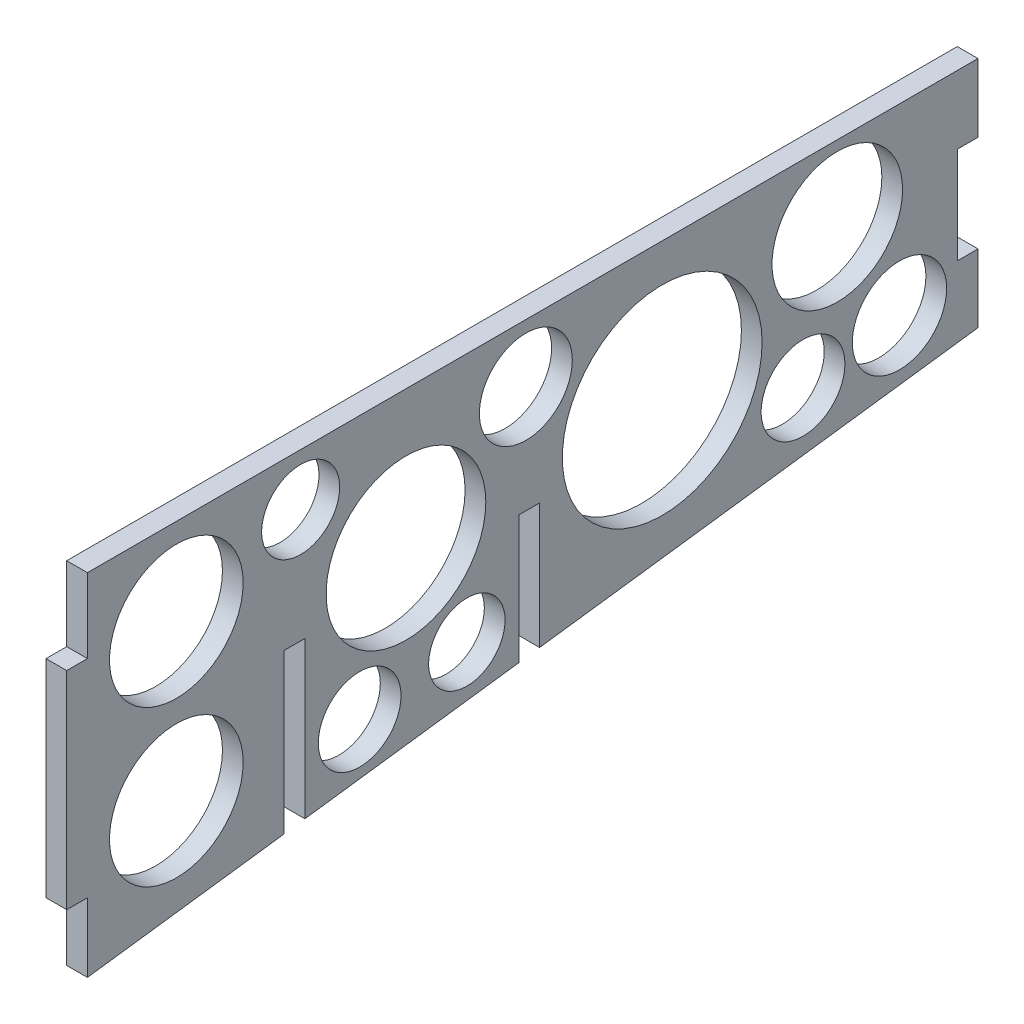
SolidWorks part; units mm, degrees
ref_plane "Front Plane" through (0, 0, 0) normal (0, 0, 1) x (1, 0, 0)
ref_plane "Top Plane" through (0, 0, 0) normal (0, 1, 0) x (1, 0, 0)
ref_plane "Right Plane" through (0, 0, 0) normal (1, 0, 0) x (0, 0, -1)
sketch "Sketch1" plane through (0, 0, 0) normal (1, 0, 0) x (0, 0, -1)
  line L0 (0, 0) -> (0, -50.7777)
  line L1 (0, -50.7777) -> (129, -33.7689)
  line L2 (129, -33.7689) -> (129, 0)
  line L3 (0, 0) -> (129, 0)
  dimension "D1" = 129
  dimension "D2" = 50.7777
  dimension "D3" = 33.7689
extrude "Boss-Extrude1" add sketch "Sketch1" along normal blind 3
sketch "Sketch2" plane through (3, 0, 0) normal (1, 0, 0) x (0, 0, -1)
  line L1 (28.5, -24) -> (31.5, -24)
  line L2 (28.5, -24) -> (28.5, -52.0231)
  line L3 (28.5, -52.0231) -> (31.5, -52.0231)
  line L4 (31.5, -24) -> (31.5, -52.0231)
  line L5 (0, 0) -> (0, -50.7777) construction
  line L6 (0, 0) -> (0, -50.7777) construction
  line L8 (30, -24) -> (30, 0) construction
  line L9 (129, 0) -> (0, 0) construction
  line L11 (62.5, -24) -> (65.5, -24)
  line L12 (62.5, -24) -> (62.5, -45.366)
  line L13 (62.5, -45.366) -> (65.5, -45.366)
  line L14 (65.5, -24) -> (65.5, -45.366)
  point P5 (64, -24)
  point P7 (30, -24)
  dimension "D1" = 30
  dimension "D2" = 3
  dimension "D3" = 34
  dimension "D4" = 24
extrude "Cut-Extrude1" cut sketch "Sketch2" against normal blind 20
sketch "Sketch3" plane through (3, 0, 0) normal (1, 0, 0) x (0, 0, -1)
  line L0 (0, 0) -> (0, -50.7777) construction
  line L1 (0, -10.7777) -> (-3, -10.7777)
  line L2 (0, -10.7777) -> (0, -40.7777)
  line L3 (0, -40.7777) -> (-3, -40.7777)
  line L4 (-3, -10.7777) -> (-3, -40.7777)
  dimension "D1" = 3
  dimension "D2" = 30
  dimension "D3" = 10
extrude "Boss-Extrude2" add sketch "Sketch3" against normal blind 3
sketch "Sketch4" plane through (3, 0, 0) normal (1, 0, 0) x (0, 0, -1)
  circle A0 centre (46.1398, -19.9845) radius 11.5646
  circle A1 centre (108.619, -10.9176) radius 9.4551
  circle A2 centre (83.2598, -19.9845) radius 14.4708
  circle A3 centre (12.8789, -12.5421) radius 9.679
  circle A4 centre (12.8789, -35.053) radius 9.679
  circle A5 centre (30.8876, -7.518) radius 5.6527
  circle A6 centre (54.9604, -36.1849) radius 5.532
  circle A7 centre (39.4325, -38.1144) radius 5.9899
  circle A8 centre (63.5053, -8.4368) radius 6.7293
  circle A9 centre (103.6574, -28.6506) radius 6.0669
  circle A10 centre (117.6233, -26.5374) radius 6.8296
extrude "Cut-Extrude2" cut sketch "Sketch4" against normal through all both contours A2 | A0 | A3 | A4 | A1 | A5 | A8 | A7 | A6 | A9 | A10
sketch "Sketch5" plane through (3, 0, 0) normal (1, 0, 0) x (0, 0, -1)
  line L0 (129, -33.7689) -> (129, 0) construction
  line L1 (129, -9.8844) -> (126, -9.8844)
  line L2 (129, -9.8844) -> (129, -23.8844)
  line L3 (129, -23.8844) -> (126, -23.8844)
  line L4 (126, -9.8844) -> (126, -23.8844)
  point P6 (129, -16.8844)
  point P7 (129, -16.8844)
  dimension "D1" = 14
  dimension "D2" = 3
extrude "Cut-Extrude3" cut sketch "Sketch5" against normal blind 10
